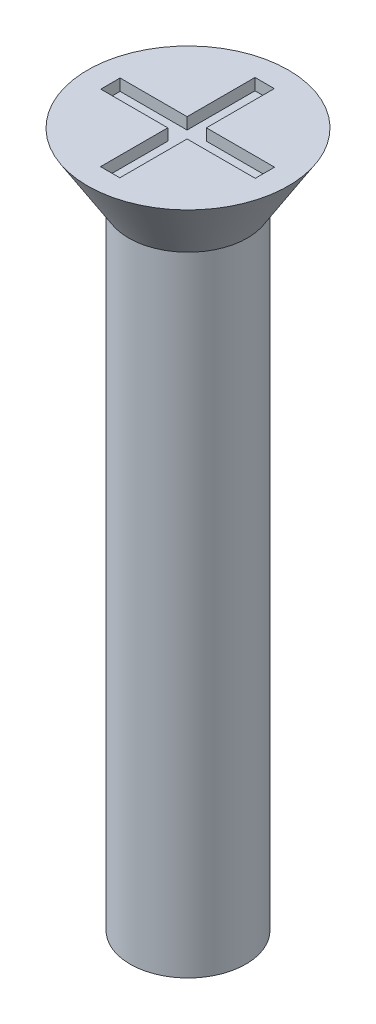
SolidWorks part; units mm, degrees
material "AISI 304"
ref_plane "Front" through (0, 0, 0) normal (0, 0, 1) x (1, 0, 0)
ref_plane "Top" through (0, 0, 0) normal (0, 1, 0) x (1, 0, 0)
ref_plane "Right" through (0, 0, 0) normal (1, 0, 0) x (0, 0, -1)
sketch "Sketch1" plane through (0, 0, 0) normal (0, 1, 0) x (1, 0, 0)
  circle A0 centre (0, 0) radius 1.5
  dimension "D1" = 3
extrude "Boss-Extrude1" add sketch "Sketch1" along normal blind 18
sketch "Sketch2" plane through (0, 18, 0) normal (0, 1, 0) x (1, 0, 0)
  circle A0 centre (0, 0) radius 2.6
  dimension "D1" = 5.2
extrude "Boss-Extrude2" add sketch "Sketch2" against normal blind 1.7 draft 32
sketch "Sketch3" plane through (0, 18, 0) normal (0, 1, 0) x (1, 0, 0)
  line L1 (-2, 0.2416) -> (2, 0.2416)
  line L2 (-2, 0.2416) -> (-2, -0.2584)
  line L3 (-2, -0.2584) -> (2, -0.2584)
  line L4 (2, 0.2416) -> (2, -0.2584)
  line L5 (-0.2653, 2) -> (0.2347, 2)
  line L6 (-0.2653, 2) -> (-0.2653, -2)
  line L7 (-0.2653, -2) -> (0.2347, -2)
  line L8 (0.2347, 2) -> (0.2347, -2)
  circle A0 centre (0, 0) radius 2.6 construction
  dimension "D1" = 0.5
  dimension "D2" = 0.5
  dimension "D3" = 4
  dimension "D4" = 4
  dimension "D5" = 2
  dimension "D6" = 2
extrude "Cut-Extrude1" cut sketch "Sketch3" against normal blind 0.3 contours L8 L5 L6 L1 | L8 L3 L6 L7 | L6 L1 L2 L3 | L1 L8 L3 L4 | L8 L1 L6 L3
